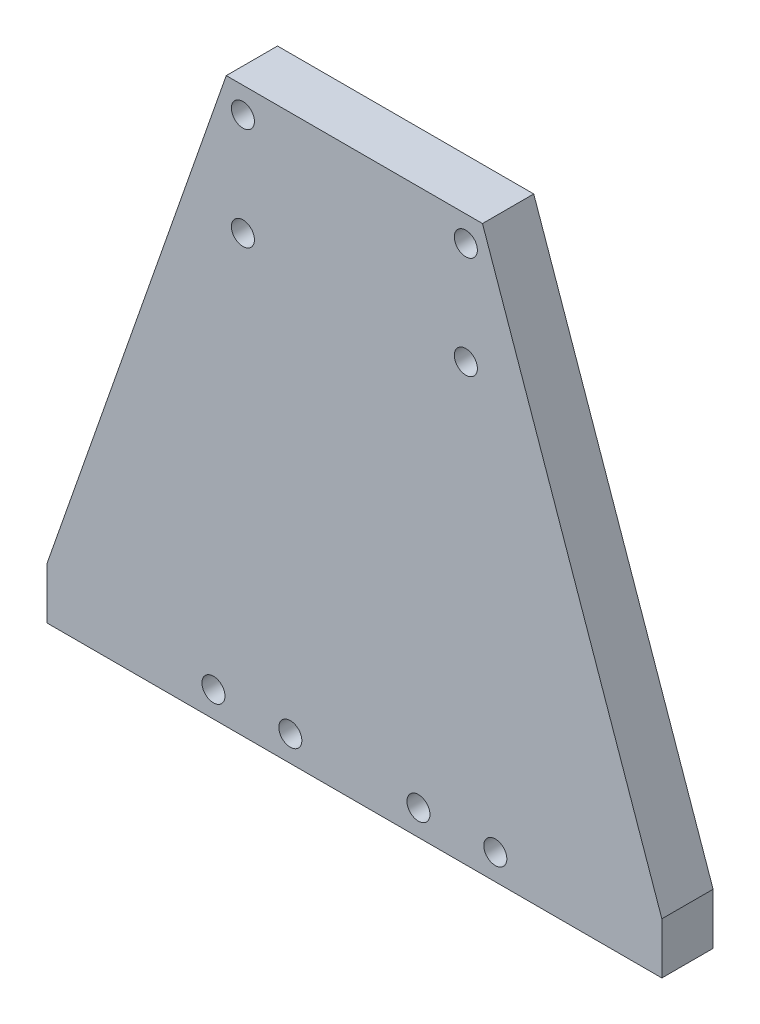
SolidWorks part; units mm, degrees
ref_plane "Front" through (0, 0, 0) normal (0, 0, 1) x (1, 0, 0)
ref_plane "Top" through (0, 0, 0) normal (0, 1, 0) x (1, 0, 0)
ref_plane "Right" through (0, 0, 0) normal (1, 0, 0) x (0, 0, -1)
sketch "Sketch1" plane through (0, 0, 0) normal (0, 0, 1) x (1, 0, 0)
  line L0 (0, 0) -> (0, 97.7126) construction
  line L1 (-60, -5) -> (60, -5)
  line L2 (-60, -5) -> (-60, 5)
  line L4 (60, -5) -> (60, 5)
  line L5 (-60, -5) -> (60, 5) construction
  line L6 (-60, 5) -> (60, -5) construction
  line L7 (-60, 5) -> (-25, 105)
  line L8 (-25, 105) -> (25, 105)
  line L12 (-25, 105) -> (16.3698, 92.9408) construction
  line L13 (-7.0204, 95.6661) -> (25, 105) construction
  line L14 (60, 5) -> (25, 105)
  circle A0 centre (27.5, 0) radius 2.25
  circle A1 centre (12.5, 0) radius 2.25
  circle A2 centre (-12.5, 0) radius 2.25
  circle A3 centre (-27.5, 0) radius 2.25
  point P0 (0, 0)
  point P20 (21.6844, 0)
  dimension "D8" = 4.5
  dimension "D1" = 32.5
  dimension "D2" = 120
  dimension "D3" = 50
  dimension "D4" = 10
  dimension "D5" = 32.5
  dimension "D6" = 15
  dimension "D7" = 15
extrude "Boss-Extrude1" add sketch "Sketch1" along normal blind 10
sketch "Sketch2" plane through (0, 0, 10) normal (0, 0, 1) x (1, 0, 0)
  line L0 (0, 105) -> (0, -5) construction
  line L1 (25, 105) -> (-25, 105) construction
  line L2 (-60, -5) -> (60, -5) construction
  line L3 (-35.5, 75) -> (35.5, 75)
  line L4 (-25, 105) -> (-60, 5) construction
  line L5 (60, 5) -> (25, 105) construction
  circle A0 centre (-21.75, 100) radius 2.25
  circle A1 centre (-21.75, 80) radius 2.25
  circle A2 centre (21.75, 80) radius 2.25
  circle A3 centre (21.75, 100) radius 2.25
  dimension "D5" = 4.5
  dimension "D6" = 4.5
  dimension "D1" = 5
  dimension "D2" = 20
  dimension "D3" = 30
  dimension "D4" = 3.25
extrude "Cut-Extrude1" cut sketch "Sketch2" against normal through all contours A1 | A2 | A3 | A0
